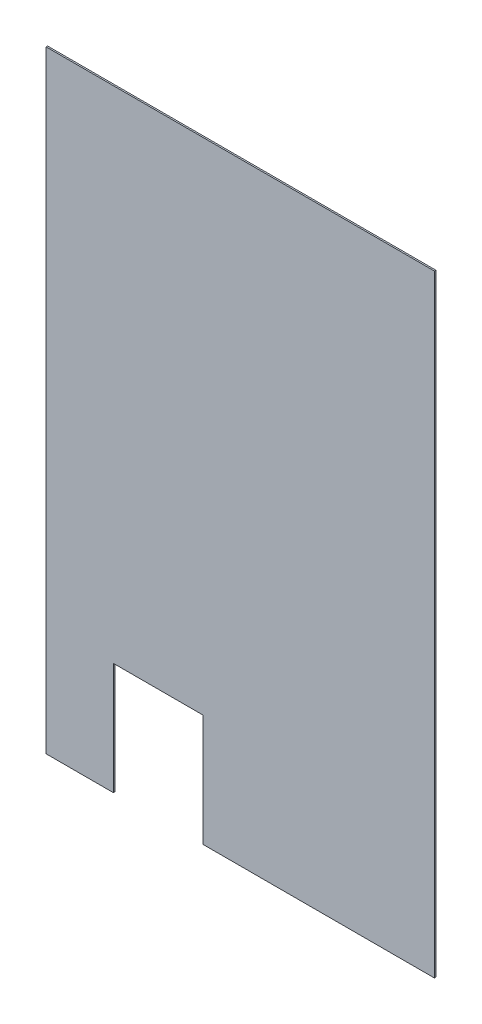
SolidWorks part; units mm, degrees
ref_plane "Front Plane" through (0, 0, 0) normal (0, 0, 1) x (1, 0, 0)
ref_plane "Top Plane" through (0, 0, 0) normal (0, 1, 0) x (1, 0, 0)
ref_plane "Right Plane" through (0, 0, 0) normal (1, 0, 0) x (0, 0, -1)
sketch "Sketch1" plane through (0, 0, 0) normal (0, 0, 1) x (1, 0, 0)
  line L0 (266.7, 0) -> (660.4, 0)
  line L1 (0, 0) -> (114.3, 0)
  line L2 (0, 0) -> (0, 1041.4)
  line L3 (0, 1041.4) -> (660.4, 1041.4)
  line L4 (660.4, 0) -> (660.4, 1041.4)
  line L6 (114.3, 0) -> (114.3, 190.5)
  line L7 (114.3, 190.5) -> (266.7, 190.5)
  line L8 (266.7, 0) -> (266.7, 190.5)
  dimension "D1" = 660.4
  dimension "D2" = 1041.4
  dimension "D3" = 190.5
  dimension "D4" = 114.3
  dimension "D5" = 393.7
extrude "Boss-Extrude1" add sketch "Sketch1" along normal blind 2.54
